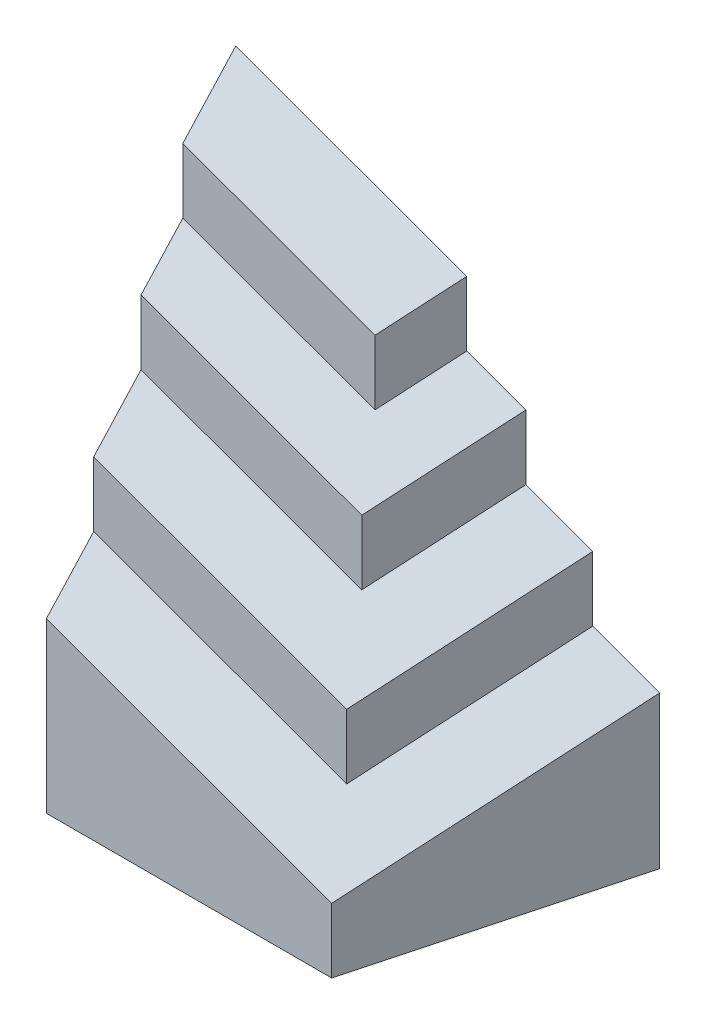
SolidWorks part; units mm, degrees
other "Perspective"
ref_plane "Front" through (0, 0, 0) normal (0, 0, 1) x (1, 0, 0)
ref_plane "Top" through (0, 0, 0) normal (0, 1, 0) x (1, 0, 0)
ref_plane "Right" through (0, 0, 0) normal (1, 0, 0) x (0, 0, -1)
sketch "Sketch1" plane through (0, 0, 0) normal (0, 1, 0) x (1, 0, 0)
  line L0 (0, 0) -> (18.2205, 68)
  line L1 (18.2205, 68) -> (-93.2205, 68)
  line L2 (-93.2205, 68) -> (-75, 0)
  line L3 (-75, 0) -> (0, 0)
  dimension "D1" = 75
  dimension "D2" = 75
  dimension "D3" = 75
  dimension "D4" = 68
extrude "Extrude1" add sketch "Sketch1" along normal blind 90
sketch "Sketch2" plane through (0, 0, -68) normal (0, 0, -1) x (-1, 0, 0)
  line L0 (-18.2205, 40) -> (93.2205, 80.5612)
  line L1 (-18.2205, 90) -> (-18.2205, 0) construction
  line L2 (93.2205, 90) -> (93.2205, 0) construction
  line L3 (-18.2205, 0) -> (93.2205, 0) construction
  line L4 (93.2205, 80.5612) -> (93.2205, 90)
  line L5 (93.2205, 90) -> (-18.2205, 90)
  line L6 (-18.2205, 90) -> (-18.2205, 40)
  dimension "D1" = 40
  dimension "D2" = 20
extrude "Cut-Extrude1" cut sketch "Sketch2" against normal through all
sketch "Sketch3" plane through (0, 0, 0) normal (0, 0, 1) x (1, 0, 0)
  line L0 (0, 46.6317) -> (0, 0) construction
  point P0 (0, 17)
  dimension "D1" = 17
ref_plane "Plane1" through (4.6791, 12.8558, 5.602) normal (0.3165, 0.8696, 0.3789) x (-0.9486, 0.2902, 0.1264)
sketch "Sketch4" plane through (4.6791, 12.8558, 5.602) normal (0.3165, 0.8696, 0.3789) x (-0.9486, 0.2902, 0.1264)
  line L1 (-37.7978, 1.4305) -> (120.9643, 1.4305)
  line L2 (-37.7978, 1.4305) -> (-37.7978, -99.709)
  line L3 (-37.7978, -99.709) -> (120.9643, -99.709)
  line L4 (120.9643, 1.4305) -> (120.9643, -99.709)
extrude "Cut-Extrude2" cut sketch "Sketch4" along normal blind 30
sketch "Sketch5" plane through (0, 0, 0) normal (0, 1, 0) x (1, 0, 0)
  line L0 (0.6209, 68) -> (-13.0446, 17)
  line L1 (18.2205, 68) -> (-93.2205, 68) construction
  line L2 (-13.0446, 17) -> (-79.5551, 17)
  line L3 (-93.2205, 68) -> (-75, 0) construction
  line L4 (-79.5551, 17) -> (-93.2205, 68)
  line L5 (-93.2205, 68) -> (0.6209, 68)
  line L6 (0, 0) -> (18.2205, 68) construction
  line L7 (-75, 0) -> (0, 0) construction
  dimension "D1" = 17
  dimension "D2" = 17
extrude "Extrude2" add sketch "Sketch5" along normal blind 100
sketch "Sketch6" plane through (0, 0, -68) normal (0, 0, -1) x (-1, 0, 0)
  line L1 (-0.6209, 63.4058) -> (93.2205, 97.5612)
  line L2 (-18.2205, 40) -> (-0.6209, 46.4058) construction
  line L3 (-0.6209, 63.4058) -> (-0.6209, 100)
  line L4 (-0.6209, 100) -> (93.2205, 100)
  line L5 (93.2205, 100) -> (93.2205, 97.5612)
extrude "Cut-Extrude3" cut sketch "Sketch6" against normal through all
sketch "Sketch7" plane through (0, 0, -17) normal (0, 0, 1) x (1, 0, 0)
  line L0 (-13.0446, 68.3796) -> (-13.0446, 29.1558) construction
  point P0 (-13.0446, 46.1558)
  dimension "D1" = 17
ref_plane "Plane2" through (9.3582, 25.7116, 11.2041) normal (0.3165, 0.8696, 0.3789) x (-0.9486, 0.2902, 0.1264)
sketch "Sketch8" plane through (9.3582, 25.7116, 11.2041) normal (0.3165, 0.8696, 0.3789) x (-0.9486, 0.2902, 0.1264)
  line L1 (-24.7709, -21.2359) -> (117.6027, -21.2359)
  line L2 (-24.7709, -21.2359) -> (-24.7709, -110.906)
  line L3 (-24.7709, -110.906) -> (117.6027, -110.906)
  line L4 (117.6027, -21.2359) -> (117.6027, -110.906)
extrude "Cut-Extrude4" cut sketch "Sketch8" along normal blind 20
sketch "Sketch9" plane through (0, 0, 0) normal (0, 1, 0) x (1, 0, 0)
  line L0 (-16.9788, 68) -> (-26.0891, 34)
  line L1 (0.6209, 68) -> (-93.2205, 68) construction
  line L2 (-26.0891, 34) -> (-84.1103, 34)
  line L3 (-93.2205, 68) -> (-79.5551, 17) construction
  line L4 (-84.1103, 34) -> (-93.2205, 68)
  line L5 (-93.2205, 68) -> (-16.9788, 68)
  line L6 (-13.0446, 17) -> (0.6209, 68) construction
  line L7 (-13.0446, 17) -> (-79.5551, 17) construction
  line L8 (-79.5551, 17) -> (-13.0446, 17) construction
  dimension "D1" = 17
  dimension "D2" = 17
extrude "Extrude3" add sketch "Sketch9" along normal blind 120
sketch "Sketch10" plane through (0, 0, -68) normal (0, 0, -1) x (-1, 0, 0)
  line L1 (16.9788, 86.8115) -> (93.2205, 114.5612)
  line L2 (93.2205, 120) -> (93.2205, 0) construction
  line L3 (93.2205, 114.5612) -> (93.2205, 120)
  line L4 (93.2205, 120) -> (16.9788, 120)
  line L5 (16.9788, 120) -> (16.9788, 86.8115)
  line L7 (-0.6209, 63.4058) -> (16.9788, 69.8115) construction
extrude "Cut-Extrude5" cut sketch "Sketch10" against normal through all
sketch "Sketch11" plane through (0, 0, -34) normal (0, 0, 1) x (1, 0, 0)
  line L0 (-26.0891, 90.1274) -> (-26.0891, 58.3115) construction
  point P0 (-26.0891, 75.3115)
  dimension "D1" = 17
ref_plane "Plane3" through (14.0374, 38.5674, 16.8061) normal (0.3165, 0.8696, 0.3789) x (-0.9486, 0.2902, 0.1264)
sketch "Sketch12" plane through (14.0374, 38.5674, 16.8061) normal (0.3165, 0.8696, 0.3789) x (-0.9486, 0.2902, 0.1264)
  line L1 (-29.3511, -21.8007) -> (119.4121, -21.8007)
  line L2 (-29.3511, -21.8007) -> (-29.3511, -110.8759)
  line L3 (-29.3511, -110.8759) -> (119.4121, -110.8759)
  line L4 (119.4121, -21.8007) -> (119.4121, -110.8759)
extrude "Cut-Extrude6" cut sketch "Sketch12" along normal blind 20
sketch "Sketch13" plane through (0, 0, 0) normal (0, 1, 0) x (1, 0, 0)
  line L0 (-93.2205, 68) -> (-32.508, 68)
  line L1 (-16.9788, 68) -> (-93.2205, 68) construction
  line L2 (-32.508, 68) -> (-37.599, 49)
  line L3 (-37.599, 49) -> (-88.1295, 49)
  line L4 (-93.2205, 68) -> (-84.1103, 34) construction
  line L5 (-88.1295, 49) -> (-93.2205, 68)
  line L6 (-16.9788, 68) -> (-26.0891, 34) construction
  line L7 (-26.0891, 34) -> (-84.1103, 34) construction
  line L8 (-26.0891, 34) -> (-16.9788, 68) construction
  line L9 (-84.1103, 34) -> (-26.0891, 34) construction
  dimension "D1" = 15
  dimension "D2" = 15
extrude "Extrude4" add sketch "Sketch13" along normal blind 140
sketch "Sketch14" plane through (0, 0, -68) normal (0, 0, -1) x (-1, 0, 0)
  line L1 (32.508, 109.4637) -> (93.2205, 131.5612)
  line L2 (93.2205, 140) -> (93.2205, 0) construction
  line L3 (16.9788, 86.8115) -> (32.508, 92.4637) construction
  line L4 (93.2205, 131.5612) -> (93.2205, 140)
  line L5 (93.2205, 140) -> (32.508, 140)
  line L6 (32.508, 140) -> (32.508, 109.4637)
extrude "Cut-Extrude7" cut sketch "Sketch14" against normal through all
sketch "Sketch15" plane through (0, 0, -49) normal (0, 0, 1) x (1, 0, 0)
  line L0 (-37.599, 111.3167) -> (-37.599, 86.0372) construction
  point P0 (-37.599, 103.0372)
  dimension "D1" = 17
ref_plane "Plane4" through (18.7165, 51.4231, 22.4082) normal (0.3165, 0.8696, 0.3789) x (-0.9486, 0.2902, 0.1264)
sketch "Sketch16" plane through (18.7165, 51.4231, 22.4082) normal (0.3165, 0.8696, 0.3789) x (-0.9486, 0.2902, 0.1264)
  line L1 (25.3273, -67.6179) -> (133.4204, -67.6179)
  line L2 (25.3273, -67.6179) -> (25.3273, -120.2586)
  line L3 (25.3273, -120.2586) -> (133.4204, -120.2586)
  line L4 (133.4204, -67.6179) -> (133.4204, -120.2586)
extrude "Cut-Extrude8" cut sketch "Sketch16" along normal blind 10
